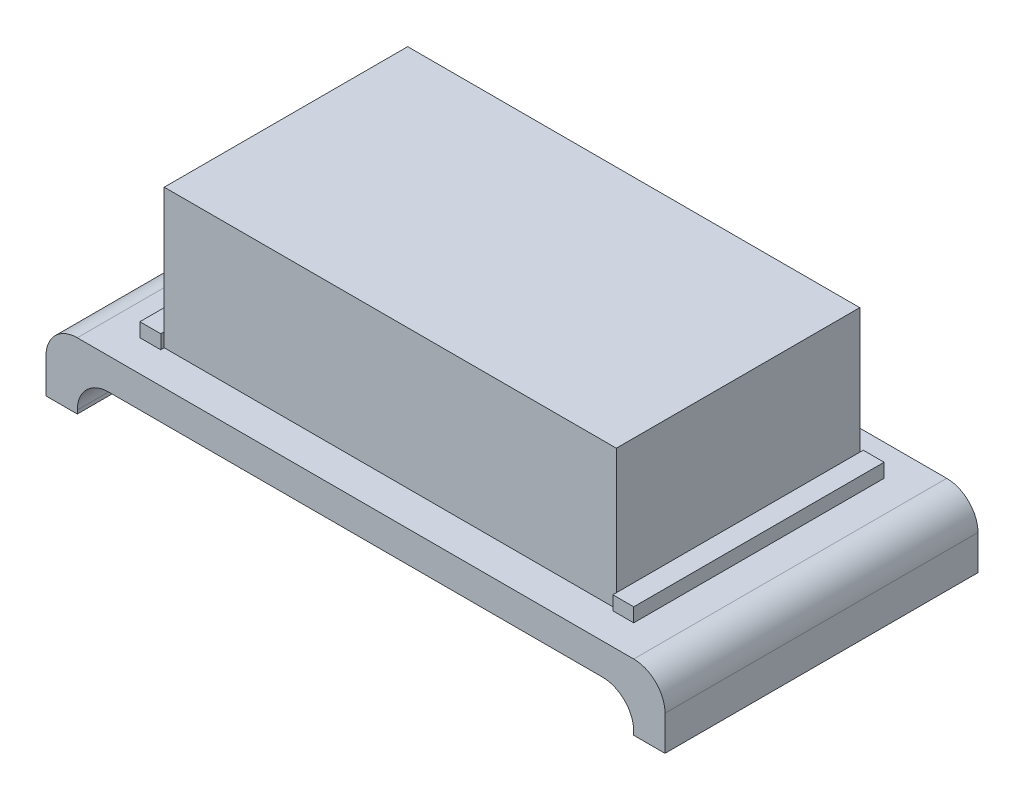
SolidWorks part; units mm, degrees
ref_plane "Plan de face" through (0, 0, 0) normal (0, 0, 1) x (1, 0, 0)
ref_plane "Plan de dessus" through (0, 0, 0) normal (0, 1, 0) x (1, 0, 0)
ref_plane "Plan de droite" through (0, 0, 0) normal (1, 0, 0) x (0, 0, -1)
sketch "Esquisse1" plane through (0, 0, 0) normal (0, 1, 0) x (1, 0, 0)
  line L1 (-46.1375, 23.6603) -> (83.8625, 23.6603)
  line L2 (-46.1375, 23.6603) -> (-46.1375, -46.3397)
  line L3 (-46.1375, -46.3397) -> (83.8625, -46.3397)
  line L4 (83.8625, 23.6603) -> (83.8625, -46.3397)
  dimension "D1" = 130
  dimension "D2" = 70
sketch "Esquisse2" plane through (0, 0, 0) normal (0, 1, 0) x (1, 0, 0)
  line L0 (-46.1375, 23.6603) -> (-46.1375, -46.3397) construction
  line L1 (-61.1375, 33.6603) -> (98.8625, 33.6603)
  line L2 (-61.1375, 33.6603) -> (-61.1375, -56.3397)
  line L3 (-61.1375, -56.3397) -> (98.8625, -56.3397)
  line L4 (98.8625, 33.6603) -> (98.8625, -56.3397)
  line L5 (83.8625, 23.6603) -> (83.8625, -46.3397) construction
  line L6 (-46.1375, 23.6603) -> (83.8625, 23.6603) construction
  line L7 (-46.1375, -46.3397) -> (83.8625, -46.3397) construction
  dimension "D1" = 15
  dimension "D2" = 15
  dimension "D3" = 10
  dimension "D4" = 10
  dimension "D5" = 90
  dimension "D6" = 160
extrude "Extrusion1" add sketch "Esquisse2" against normal blind 9
extrude "Beurre (avec marges)" add sketch "Esquisse1" along normal blind 40
sketch "Esquisse4" plane through (0, 0, 0) normal (0, 1, 0) x (1, 0, 0)
  line L0 (-46.1375, 23.6603) -> (-46.1375, -46.3397) construction
  line L1 (-46.1375, 24.6603) -> (-52.1375, 24.6603)
  line L2 (-46.1375, 24.6603) -> (-46.1375, -47.3397)
  line L3 (-46.1375, -47.3397) -> (-52.1375, -47.3397)
  line L4 (-52.1375, 24.6603) -> (-52.1375, -47.3397)
  line L6 (83.8625, 23.6603) -> (-46.1375, 23.6603) construction
  line L7 (18.8625, 33.6603) -> (18.8625, -56.3397) construction
  line L8 (98.8625, 33.6603) -> (-61.1375, 33.6603) construction
  line L9 (-61.1375, -56.3397) -> (98.8625, -56.3397) construction
  line L10 (89.8625, 24.6603) -> (89.8625, -47.3397)
  line L11 (83.8625, -47.3397) -> (89.8625, -47.3397)
  line L12 (83.8625, 24.6603) -> (83.8625, -47.3397)
  line L13 (83.8625, 24.6603) -> (89.8625, 24.6603)
  dimension "D1" = 72
  dimension "D2" = 6
  dimension "D3" = 1
extrude "Extrusion3" add sketch "Esquisse4" along normal blind 4
sketch "Esquisse6" plane through (0, 0, 0) normal (0, 1, 0) x (1, 0, 0)
  line L1 (-61.1375, 33.6603) -> (-70.1375, 33.6603)
  line L2 (-61.1375, 33.6603) -> (-61.1375, -56.3397)
  line L3 (-61.1375, -56.3397) -> (-70.1375, -56.3397)
  line L4 (-70.1375, 33.6603) -> (-70.1375, -56.3397)
  line L5 (98.8625, 33.6603) -> (107.8625, 33.6603)
  line L6 (98.8625, 33.6603) -> (98.8625, -56.3397)
  line L7 (98.8625, -56.3397) -> (107.8625, -56.3397)
  line L8 (107.8625, 33.6603) -> (107.8625, -56.3397)
  dimension "D1" = 9
  dimension "D2" = 9
extrude "Extrusion4" add sketch "Esquisse6" against normal blind 19
fillet "Congé1" radius 9 4 edges at (107.8625, 0, 11.3397) (-70.1375, 0, 11.3397)
fillet "Congé2" [suppressed] radius 5
